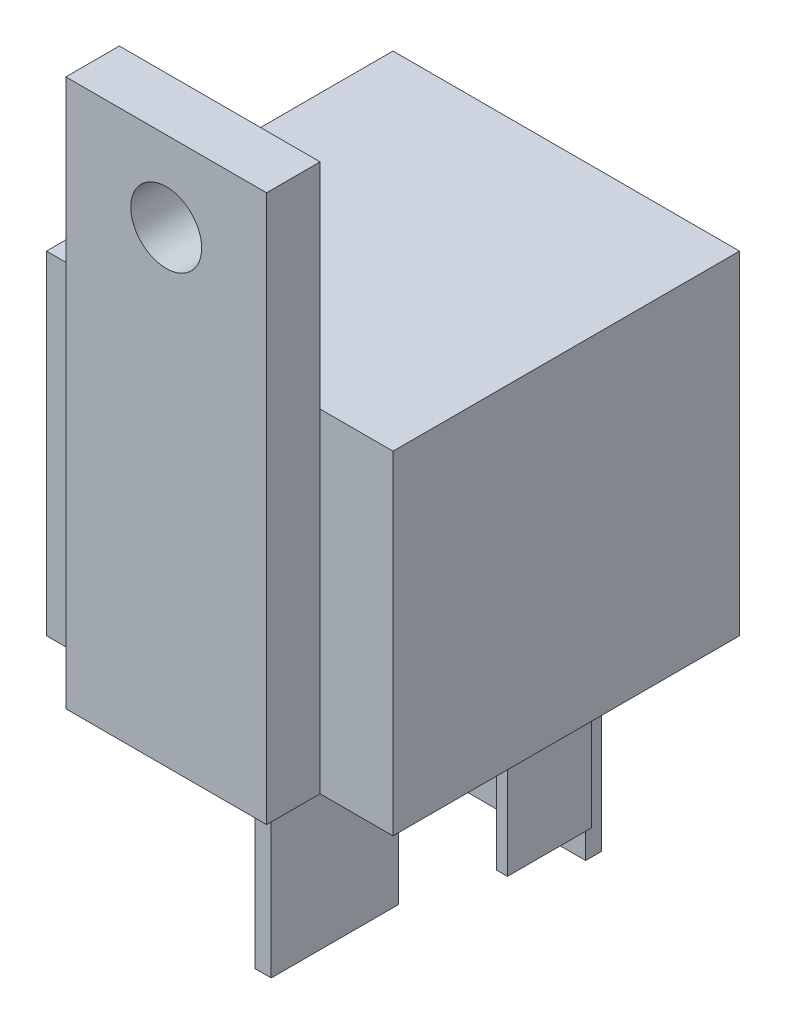
SolidWorks part; units mm, degrees
ref_plane "Front Plane" through (0, 0, 0) normal (0, 0, 1) x (1, 0, 0)
ref_plane "Top Plane" through (0, 0, 0) normal (0, 1, 0) x (1, 0, 0)
ref_plane "Right Plane" through (0, 0, 0) normal (1, 0, 0) x (0, 0, -1)
sketch "Sketch1" plane through (0, 0, 0) normal (0, 1, 0) x (1, 0, 0)
  line L1 (0, 0) -> (25.9, 0)
  line L2 (0, 0) -> (0, 25.9)
  line L3 (0, 25.9) -> (25.9, 25.9)
  line L4 (25.9, 0) -> (25.9, 25.9)
  dimension "D1" = 25.9
  dimension "D2" = 25.9
extrude "Boss-Extrude1" add sketch "Sketch1" along normal blind 24.9
sketch "Sketch2" plane through (0, 0, 0) normal (0, 0, 1) x (1, 0, 0)
  line L0 (0, 0) -> (25.9, 0) construction
  line L1 (5.45, 0) -> (20.45, 0)
  line L2 (5.45, 0) -> (5.45, 40.9)
  line L3 (5.45, 40.9) -> (20.45, 40.9)
  line L4 (20.45, 0) -> (20.45, 40.9)
  line L6 (0, 24.9) -> (25.9, 24.9) construction
  circle A0 centre (12.95, 34.9) radius 2.65
  point P6 (12.95, 0)
  point P7 (12.95, 0)
  dimension "D4" = 5.3
  dimension "D1" = 15
  dimension "D2" = 16
  dimension "D3" = 6
extrude "Boss-Extrude2" add sketch "Sketch2" along normal blind 4
sketch "Sketch3" plane through (0, 0, 0) normal (0, -1, 0) x (1, 0, 0)
  line L0 (25.9, -25.9) -> (0, -25.9) construction
  line L1 (17.7, -22.6) -> (8.2, -22.6)
  line L2 (17.7, -22.6) -> (17.7, -23.8)
  line L3 (17.7, -23.8) -> (8.2, -23.8)
  line L4 (8.2, -22.6) -> (8.2, -23.8)
  line L5 (12.95, -25.9) -> (12.95, 4) construction
  line L6 (21.8, -18.95) -> (21, -18.95)
  line L7 (21.8, -18.95) -> (21.8, -12.65)
  line L8 (21.8, -12.65) -> (21, -12.65)
  line L9 (21, -18.95) -> (21, -12.65)
  line L10 (5.45, 4) -> (20.45, 4) construction
  line L11 (4.1, -12.65) -> (4.9, -12.65)
  line L12 (4.9, -18.95) -> (4.9, -12.65)
  line L13 (4.1, -18.95) -> (4.9, -18.95)
  line L14 (4.1, -18.95) -> (4.1, -12.65)
  line L16 (13.55, -3.25) -> (12.35, -3.25)
  line L17 (13.55, -3.25) -> (13.55, -12.75)
  line L18 (13.55, -12.75) -> (12.35, -12.75)
  line L19 (12.35, -3.25) -> (12.35, -12.75)
  point P4 (12.95, -23.8)
  point P7 (12.95, -25.9)
  point P8 (17.7, -23.2)
  point P17 (21.8, -15.8)
  point P18 (21.4, -18.95)
  point P27 (12.95, -3.25)
  point P28 (13.55, -8)
  dimension "D1" = 1.2
  dimension "D2" = 9.5
  dimension "D3" = 2.7
  dimension "D4" = 7.4
  dimension "D5" = 6.3
  dimension "D6" = 0.8
  dimension "D7" = 8.45
  dimension "D8" = 17.9
extrude "Boss-Extrude3" add sketch "Sketch3" along normal blind 11
sketch "Sketch5" plane through (0, -11, 0) normal (0, -1, 0) x (1, 0, 0)
  line L0 (13.55, -12.75) -> (13.55, -3.25) construction
  line L1 (13.55, -3.25) -> (12.35, -3.25) construction
  line L2 (12.35, -3.25) -> (12.35, -12.75) construction
  line L3 (12.35, -12.75) -> (13.55, -12.75) construction
  line L4 (17.7, -23.8) -> (17.7, -22.6) construction
  line L5 (17.7, -22.6) -> (8.2, -22.6) construction
  line L6 (8.2, -22.6) -> (8.2, -23.8) construction
  line L7 (8.2, -23.8) -> (17.7, -23.8) construction
  line L8 (13.55, -12.75) -> (13.55, -3.25)
  line L9 (13.55, -3.25) -> (12.35, -3.25)
  line L10 (12.35, -3.25) -> (12.35, -12.75)
  line L11 (12.35, -12.75) -> (13.55, -12.75)
  line L12 (17.7, -23.8) -> (17.7, -22.6)
  line L13 (17.7, -22.6) -> (8.2, -22.6)
  line L14 (8.2, -22.6) -> (8.2, -23.8)
  line L15 (8.2, -23.8) -> (17.7, -23.8)
extrude "Boss-Extrude4" add sketch "Sketch5" along normal blind 6
